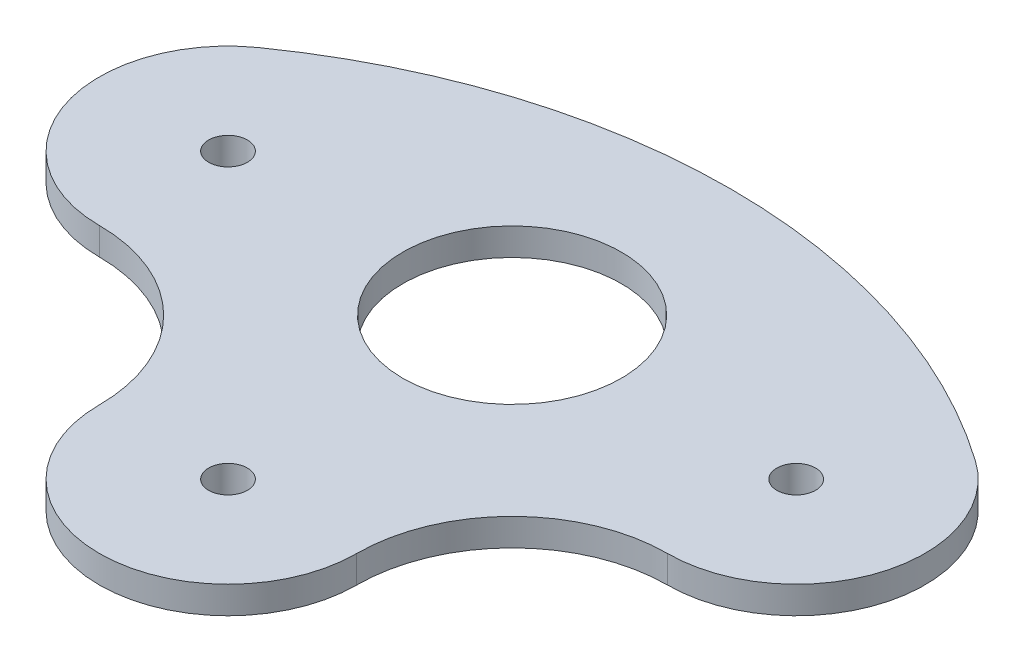
SolidWorks part; units mm, degrees
ref_plane "Front Plane" through (0, 0, 0) normal (0, 0, 1) x (1, 0, 0)
ref_plane "Top Plane" through (0, 0, 0) normal (0, 1, 0) x (1, 0, 0)
ref_plane "Right Plane" through (0, 0, 0) normal (1, 0, 0) x (0, 0, -1)
sketch "Sketch1" plane through (0, 0, 0) normal (0, 1, 0) x (1, 0, 0)
  circle A0 centre (0, 0) radius 12.7
  circle A1 centre (-33, 0) radius 2.25
  circle A2 centre (33, 0) radius 2.25
  circle A3 centre (0, -33) radius 2.25
  arc A4 (-33, 0) -> (33, 0) centre (0, 0) ccw construction
  arc A5 (-41.6054, 12.225) -> (-33, -14.95) centre (-33, 0) ccw
  arc A6 (-14.95, -33) -> (14.95, -33) centre (0, -33) ccw
  arc A7 (33, -14.95) -> (41.6054, 12.225) centre (33, 0) ccw
  arc A8 (-33, -14.95) -> (-14.95, -33) centre (-33, -33) cw
  arc A9 (14.95, -33) -> (33, -14.95) centre (33, -33) cw
  arc A10 (-41.6054, 12.225) -> (41.6054, 12.225) centre (0, -46.8803) cw
  point P2 (0, 25.4)
  point P23 (0, 12.7)
  dimension "D1" = 4.5
  dimension "D2" = 25.4
  dimension "D4" = 12.7
  dimension "D5" = 12.7
  dimension "D3" = 33
extrude "Boss-Extrude1" add sketch "Sketch1" along normal blind 3.175
